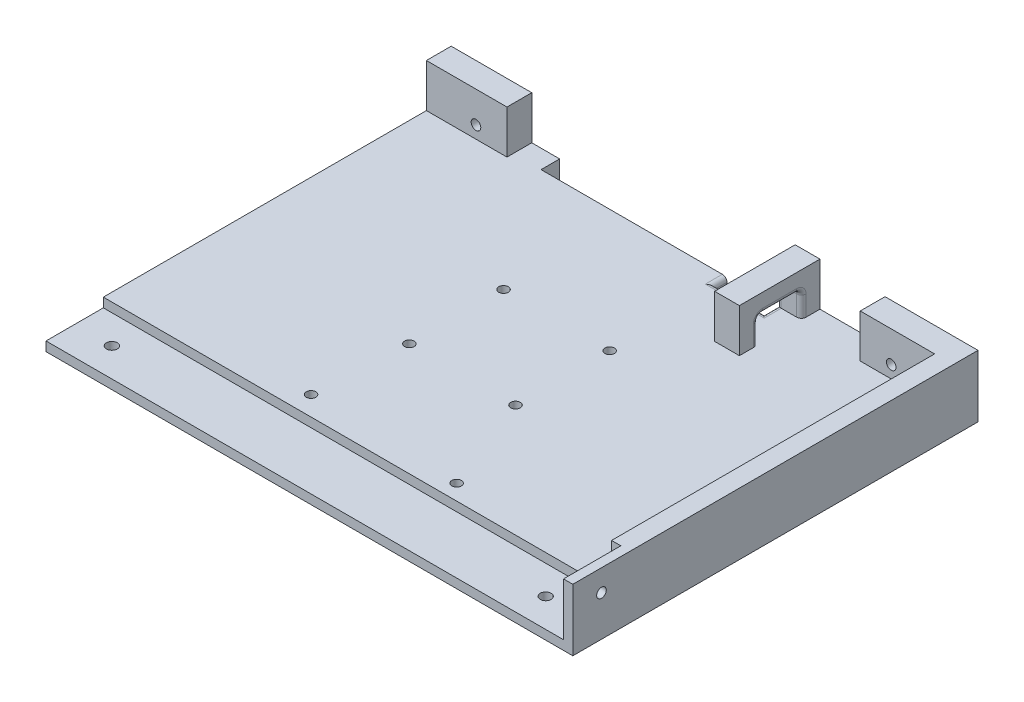
SolidWorks part; units mm, degrees
ref_plane "Front" through (0, 0, 0) normal (0, 0, 1) x (1, 0, 0)
ref_plane "Top" through (0, 0, 0) normal (0, 1, 0) x (1, 0, 0)
ref_plane "Right" through (0, 0, 0) normal (1, 0, 0) x (0, 0, -1)
sketch "Sketch1" plane through (0, 0, 0) normal (0, 1, 0) x (1, 0, 0)
  line L1 (-85, -65.375) -> (85, -65.375)
  line L2 (-85, -65.375) -> (-85, 65.375)
  line L3 (-85, 65.375) -> (85, 65.375)
  line L4 (85, -65.375) -> (85, 65.375)
  line L5 (-85, -65.375) -> (85, 65.375) construction
  line L6 (-85, 65.375) -> (85, -65.375) construction
  line L7 (-50, 65.375) -> (10, 65.375)
  line L8 (-50, 65.375) -> (-50, 59.375)
  line L9 (-50, 59.375) -> (10, 59.375)
  line L10 (10, 65.375) -> (10, 59.375)
  line L11 (-50, 65.375) -> (10, 59.375) construction
  line L12 (-50, 59.375) -> (10, 65.375) construction
  point P0 (0, 0)
  point P10 (-20, 62.375)
  dimension "D1" = 130.75
  dimension "D2" = 170
  dimension "D3" = 6
  dimension "D4" = 60
  dimension "D5" = 35
extrude "Boss-Extrude1" add sketch "Sketch1" along normal blind 6 contours L3 L10 L9 L8 L2 L1 L4
sketch "Sketch2" plane through (0, 6, 0) normal (0, 1, 0) x (1, 0, 0)
  line L0 (10, 65.375) -> (85, 65.375) construction
  line L1 (-85, 65.375) -> (-59, 65.375)
  line L2 (-85, 65.375) -> (-85, 57.375)
  line L3 (-85, 57.375) -> (-59, 57.375)
  line L4 (-59, 65.375) -> (-59, 57.375)
  line L5 (-85, 65.375) -> (-59, 57.375) construction
  line L6 (-85, 57.375) -> (-59, 65.375) construction
  line L7 (85, 65.375) -> (55, 65.375)
  line L8 (85, 65.375) -> (85, 57.375)
  line L9 (85, 57.375) -> (55, 57.375)
  line L10 (55, 65.375) -> (55, 57.375)
  line L11 (85, 65.375) -> (55, 57.375) construction
  line L12 (85, 57.375) -> (55, 65.375) construction
  point P4 (-72, 61.375)
  point P10 (70, 61.375)
  dimension "D1" = 8
  dimension "D2" = 26
  dimension "D3" = 8
  dimension "D4" = 30
extrude "Boss-Extrude2" add sketch "Sketch2" along normal blind 14
sketch "Sketch3" plane through (0, 0, -57.375) normal (0, 0, 1) x (1, 0, 0)
  line L0 (-85, 20) -> (-59, 20) construction
  line L2 (-59, 20) -> (-59, 6) construction
  line L3 (55, 20) -> (85, 20) construction
  line L4 (55, 20) -> (55, 6) construction
  circle A0 centre (-69, 10) radius 1.55
  circle A1 centre (65, 10) radius 1.55
  dimension "D1" = 3.1
  dimension "D2" = 10
  dimension "D3" = 10
  dimension "D4" = 3.1
  dimension "D5" = 10
  dimension "D6" = 10
extrude "Cut-Extrude1" cut sketch "Sketch3" against normal through all
sketch "Sketch4" plane through (0, 6, 0) normal (0, 1, 0) x (1, 0, 0)
  line L0 (85, -65.375) -> (85, 57.375) construction
  line L1 (-85, -65.375) -> (85, -65.375)
  line L2 (-85, -65.375) -> (-85, -46.875)
  line L3 (-85, -46.875) -> (85, -46.875)
  line L4 (85, -65.375) -> (85, -46.875)
  line L5 (-85, -65.375) -> (85, -46.875) construction
  line L6 (-85, -46.875) -> (85, -65.375) construction
  point P4 (0, -56.125)
  dimension "D1" = 18.5
extrude "Cut-Extrude2" cut sketch "Sketch4" against normal blind 3
sketch "Sketch5" plane through (0, 3, 0) normal (0, 1, 0) x (1, 0, 0)
  line L0 (-85, -46.875) -> (-85, -65.375) construction
  line L1 (85, -65.375) -> (85, -46.875) construction
  line L2 (-85, -65.375) -> (85, -65.375) construction
  circle A0 centre (-73, -56.125) radius 1.75
  circle A1 centre (67, -56.125) radius 1.75
  dimension "D1" = 3.5
  dimension "D2" = 3.5
  dimension "D3" = 12
  dimension "D5" = 9.25
  dimension "D4" = 18
extrude "Cut-Extrude3" cut sketch "Sketch5" against normal blind 3
sketch "Sketch7" plane through (0, 20, 0) normal (0, 1, 0) x (1, 0, 0)
  line L0 (-85, -65.375) -> (85, -65.375) construction
  line L1 (85, 65.375) -> (79, 65.375)
  line L2 (85, 65.375) -> (85, -65.375)
  line L3 (85, -65.375) -> (79, -65.375)
  line L4 (79, 65.375) -> (79, -65.375)
  line L5 (85, 65.375) -> (79, -65.375) construction
  line L6 (85, -65.375) -> (79, 65.375) construction
  line L7 (85, -46.875) -> (-85, -46.875) construction
  line L8 (79, -65.375) -> (82, -65.375)
  line L9 (79, -65.375) -> (79, -46.875)
  line L10 (79, -46.875) -> (82, -46.875)
  line L11 (82, -65.375) -> (82, -46.875)
  line L12 (79, -65.375) -> (82, -46.875) construction
  line L13 (79, -46.875) -> (82, -65.375) construction
  line L14 (85, -46.875) -> (-85, -46.875) construction
  point P4 (82, 0)
  point P11 (80.5, -56.125)
  line M5 (55, 57.375) -> (85, 57.375)
  dimension "D1" = 6
  dimension "D2" = 3
extrude "Boss-Extrude3" add sketch "Sketch7" against normal up to next contours L11 L3 L2 L4 L10 M5
sketch "Sketch8" plane through (82, 0, 0) normal (-1, 0, 0) x (0, 0, 1)
  line L1 (65.375, 20) -> (46.875, 20) construction
  line L2 (65.375, 20) -> (65.375, 6) construction
  line L3 (65.375, 6) -> (46.875, 6) construction
  line L4 (46.875, 20) -> (46.875, 6) construction
  line L5 (65.375, 20) -> (46.875, 6) construction
  line L6 (65.375, 6) -> (46.875, 20) construction
  circle A0 centre (56.125, 13) radius 1.55
  point P4 (56.125, 13)
  dimension "D1" = 3.1
extrude "Cut-Extrude4" cut sketch "Sketch8" against normal through all
sketch "Sketch9" plane through (0, 6, 0) normal (0, 1, 0) x (1, 0, 0)
  line L1 (10, 65.375) -> (26, 65.375)
  line L2 (10, 65.375) -> (10, 55.375)
  line L3 (10, 55.375) -> (26, 55.375)
  line L4 (26, 65.375) -> (26, 55.375)
  line L5 (10, 65.375) -> (26, 55.375) construction
  line L6 (10, 55.375) -> (26, 65.375) construction
  point P4 (18, 60.375)
  dimension "D1" = 10
  dimension "D2" = 16
extrude "Cut-Extrude5" cut sketch "Sketch9" against normal up to next
sketch "Sketch10" plane through (0, 6, 0) normal (0, 1, 0) x (1, 0, 0)
  line L1 (26, 65.375) -> (34, 65.375)
  line L2 (26, 65.375) -> (26, 39.375)
  line L3 (26, 39.375) -> (34, 39.375)
  line L4 (34, 65.375) -> (34, 39.375)
  line L5 (26, 65.375) -> (34, 39.375) construction
  line L6 (26, 39.375) -> (34, 65.375) construction
  point P4 (30, 52.375)
  dimension "D1" = 26
  dimension "D2" = 8
extrude "Boss-Extrude4" add sketch "Sketch10" along normal blind 14
sketch "Sketch11" plane through (34, 0, 0) normal (1, 0, 0) x (0, 0, -1)
  line L4 (45.375, 12) -> (45.375, 6)
  line L5 (39.375, 6) -> (65.375, 6) construction
  line L6 (45.375, 6) -> (59.375, 6)
  line L7 (59.375, 6) -> (59.375, 12)
  line L8 (45.375, 12) -> (59.375, 12)
  line L9 (59.375, 12) -> (59.375, 14)
  line L10 (59.375, 14) -> (45.375, 14)
  line L11 (45.375, 14) -> (45.375, 12)
  line L13 (59.375, 12) -> (59.375, 14)
  line L14 (59.375, 14) -> (45.375, 14)
  line L15 (45.375, 14) -> (45.375, 12)
  dimension "D1" = 6
extrude "Cut-Extrude6" cut sketch "Sketch11" against normal up to next
fillet "Fillet1" radius 1.5 11 edges at (30, 14, -59.375) (30, 14, -45.375) (26, 10, -45.375) (26, 14, -52.375) (10, 6, -57.375) (18, 6, -55.375) (26, 6, -57.375) (26, 10, -59.375) (34, 10, -59.375) (34, 14, -52.375) (34, 10, -45.375)
sketch "Sketch12" plane through (0, 6, 0) normal (0, 1, 0) x (1, 0, 0)
  line L0 (79, 57.375) -> (79, -46.875) construction
  line L1 (79, -46.875) -> (-85, -46.875) construction
  circle A0 centre (24, -41.875) radius 1.55
  circle A1 centre (-24.26, -40.575) radius 1.55
  dimension "D1" = 3.1
  dimension "D2" = 3.1
  dimension "D3" = 55
  dimension "D4" = 1.3
  dimension "D5" = 48.26
  dimension "D6" = 5
extrude "Cut-Extrude7" cut sketch "Sketch12" against normal blind 14
sketch "Sketch13" plane through (0, 6, 0) normal (0, 1, 0) x (1, 0, 0)
  circle A0 centre (11.6852, 19.8285) radius 1.55
  circle A1 centre (-22.5604, 19.8285) radius 1.55
  circle A2 centre (11.6852, -10.5445) radius 1.55
  circle A3 centre (-22.5604, -10.5445) radius 1.55
  dimension "D1" = 3.1
  dimension "D2" = 3.1
  dimension "D3" = 3.1
  dimension "D4" = 3.1
extrude "Cut-Extrude8" cut sketch "Sketch13" against normal up to next
